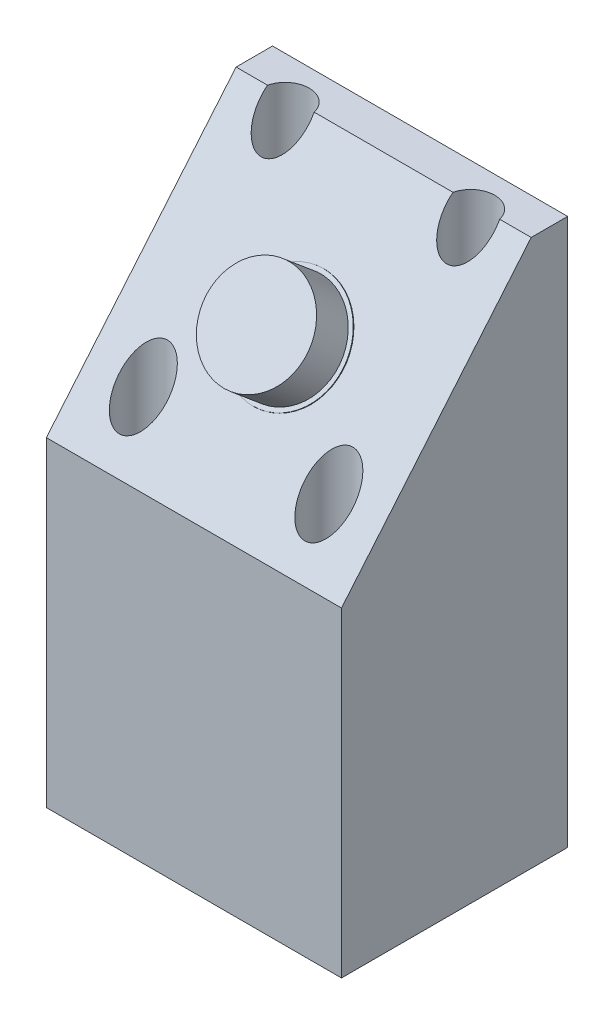
SolidWorks part; units mm, degrees
ref_plane "Ebene vorne" through (0, 0, 0) normal (0, 0, 1) x (1, 0, 0)
ref_plane "Ebene oben" through (0, 0, 0) normal (0, 1, 0) x (1, 0, 0)
ref_plane "Ebene rechts" through (0, 0, 0) normal (1, 0, 0) x (0, 0, -1)
sketch "Skizze1" plane through (0, 0, 0) normal (1, 0, 0) x (0, 0, -1)
  line L0 (0, 0) -> (22.4976, 0)
  line L1 (0, 0) -> (0, 38)
  line L2 (0, 38) -> (22.4976, 64.8116)
  line L3 (22.4976, 64.8116) -> (22.4976, 0) construction
  line L4 (22.4976, 0) -> (26.82, 0)
  line L5 (26.82, 0) -> (26.82, 64.8116)
  line L6 (26.82, 64.8116) -> (22.4976, 64.8116)
  dimension "D1" = 50
  dimension "D2" = 38
  dimension "D3" = 35
  dimension "D4" = 26.82
extrude "Aufsatz-Linear austragen1" add sketch "Skizze1" along normal blind 35
sketch "Skizze3" plane through (0, 15.7007, 18.7113) normal (0, 0.6428, 0.766) x (1, 0, 0)
  line L0 (0, 64.1097) -> (35, 29.1097) construction
  line L1 (17.5, 46.6097) -> (35, 64.1097) construction
  line L2 (35, 64.1097) -> (0, 64.1097) construction
  line L3 (35, 64.1097) -> (35, 29.1097) construction
  circle A0 centre (17.5, 46.6097) radius 6
  dimension "D1" = 12
extrude "Aufsatz-Linear austragen2" add sketch "Skizze3" along normal blind 5
sketch "Skizze4" plane through (0, 15.7007, 18.7113) normal (0, 0.6428, 0.766) x (1, 0, 0)
  circle A0 centre (17.5, 46.6097) radius 6.5
  dimension "D1" = 13
extrude "Aufsatz-Linear austragen3" add sketch "Skizze4" along normal blind 0.1
ref_plane "Ebene1" through (0, 38, 0) normal (0, -1, 0) x (-1, 0, 0)
ref_plane "Ebene2" through (0, 4.5, 0) normal (0, 1, 0) x (1, 0, 0)
sketch "Skizze7" plane through (0, 4.5, 0) normal (0, -1, 0) x (-1, 0, 0)
  line L0 (-35, 26.82) -> (0, 26.82) construction
  line L1 (-35, 0) -> (0, 26.82) construction
  line L2 (-17.5, 13.41) -> (-17.5, 26.82) construction
  line L4 (-17.5, 13.41) -> (-35, 13.41) construction
  line L5 (-35, 0) -> (-35, 26.82) construction
  circle A0 centre (-28.5, 5) radius 2.85
  circle A1 centre (-6.5, 5) radius 2.85
  circle A2 centre (-6.5, 21.82) radius 2.85
  circle A3 centre (-28.5, 21.82) radius 2.85
  dimension "D1" = 5.7
  dimension "D2" = 11
  dimension "D3" = 5
extrude "Schnitt-Linear austragen1" cut sketch "Skizze7" against normal through all
hole_wizard "Ø3.4 (3.4) Durchmesser Bohrung1" positions "3D-Skizze3" profile "Skizze8" hole size "Ø3.4" standard "DIN" end condition up to next
sketch3d "3D-Skizze3"
  line L0 (6.5, 47.3553, -5) -> (6.5, 4.5, -5) construction
  line L1 (6.5, 64.8116, -21.82) -> (6.5, 4.5, -21.82) construction
  line L2 (28.5, 64.8116, -21.82) -> (28.5, 4.5, -21.82) construction
  line L3 (28.5, 47.3553, -5) -> (28.5, 4.5, -5) construction
  point P0 (6.5, 4.5, -5)
  point P4 (6.5, 4.5, -21.82)
  point P8 (28.5, 4.5, -21.82)
  point P12 (28.5, 4.5, -5)
sketch "Skizze8" plane through (6.5, 4.5, -5) normal (1, 0, 0) x (0, 0, 1)
  line L0 (0, 0) -> (0, 4.5)
  line L1 (0, 4.5) -> (1.7, 4.5)
  line L2 (1.7, 4.5) -> (1.7, 0)
  line L5 (1.7, 0) -> (0, 0)
  line L11 (0, -6.35) -> (0, 107.95) construction
  dimension "Bohrerdurchmesser" = 3.4
  dimension "Bohrungstiefe" = 4.5
